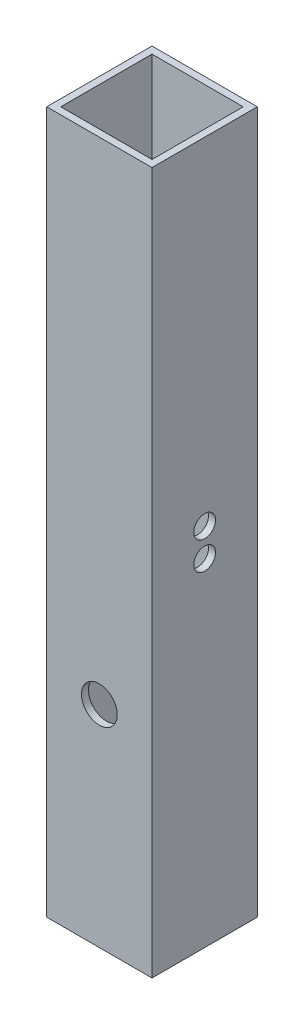
SolidWorks part; units mm, degrees
ref_plane "前视基准面" through (0, 0, 0) normal (0, 0, 1) x (1, 0, 0)
ref_plane "上视基准面" through (0, 0, 0) normal (0, 1, 0) x (1, 0, 0)
ref_plane "右视基准面" through (0, 0, 0) normal (1, 0, 0) x (0, 0, -1)
sketch "草图1" plane through (0, 0, 0) normal (0, 1, 0) x (1, 0, 0)
  line L0 (-6.5, 6.5) -> (6.5, 6.5)
  line L1 (7.5, 7.5) -> (-7.5, 7.5)
  line L2 (7.5, 7.5) -> (7.5, -7.5)
  line L3 (7.5, -7.5) -> (-7.5, -7.5)
  line L4 (-7.5, 7.5) -> (-7.5, -7.5)
  line L5 (7.5, 7.5) -> (-7.5, -7.5) construction
  line L6 (7.5, -7.5) -> (-7.5, 7.5) construction
  line L7 (6.5, 6.5) -> (6.5, -6.5)
  line L8 (6.5, -6.5) -> (-6.5, -6.5)
  line L9 (-6.5, -6.5) -> (-6.5, 6.5)
  point P0 (0, 0)
  dimension "D1" = 15
  dimension "D2" = 1
extrude "凸台-拉伸1" add sketch "草图1" along normal blind 100
sketch "草图2" plane through (0, 0, 7.5) normal (0, 0, 1) x (1, 0, 0)
  line L0 (-7.5, 0) -> (7.5, 0) construction
  line L1 (7.5, 100) -> (7.5, 0) construction
  circle A0 centre (0, 30) radius 2.55
  dimension "D1" = 5.1
  dimension "D2" = 30
  dimension "D3" = 7.5
extrude "切除-拉伸1" cut sketch "草图2" against normal blind 100
sketch "草图4" plane through (7.5, 0, 0) normal (1, 0, 0) x (0, 0, -1)
  line L0 (-7.5, 100) -> (7.5, 100) construction
  circle A0 centre (0, 52) radius 1.55
  circle A2 centre (0, 48) radius 1.55
  dimension "D3" = 3.1
  dimension "D4" = 3.1
  dimension "D1" = 48
  dimension "D2" = 4
extrude "切除-拉伸2" cut sketch "草图4" against normal up to surface (15 mm away) up to face at (-7.5, 50, 0)
